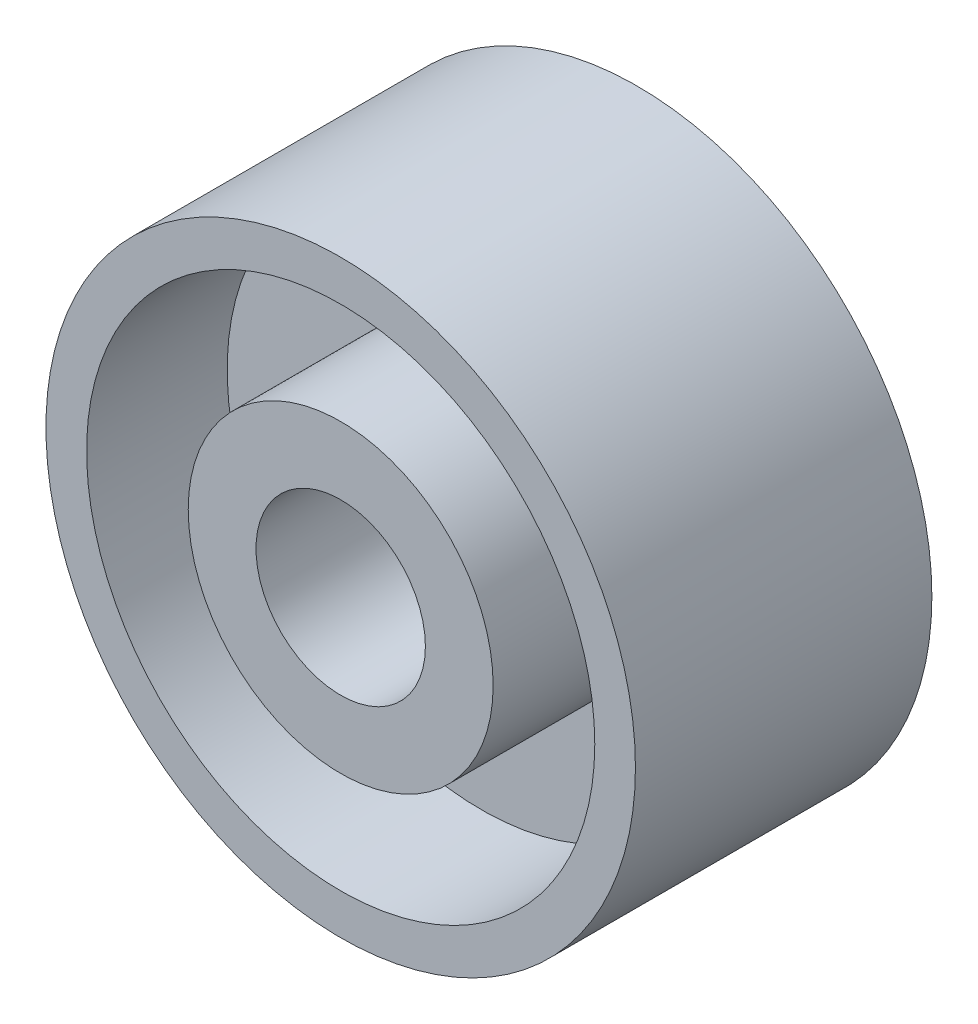
SolidWorks part; units mm, degrees
ref_plane "Front Plane" through (0, 0, 0) normal (0, 0, 1) x (1, 0, 0)
ref_plane "Top Plane" through (0, 0, 0) normal (0, 1, 0) x (1, 0, 0)
ref_plane "Right Plane" through (0, 0, 0) normal (1, 0, 0) x (0, 0, -1)
sketch "Sketch1" plane through (0, 0, 0) normal (0, 0, 1) x (1, 0, 0)
  line L0 (0, 0) -> (0, 2.4926) construction
  line L1 (0, 2.4926) -> (0, -2.9172) construction
  line L2 (0, 0) -> (4.0402, 0) construction
  line L3 (4.0402, 0) -> (-4.0539, 0) construction
  circle A0 centre (0, 0) radius 1.74
  dimension "D1" = 3.48
extrude "Boss-Extrude1" add sketch "Sketch1" against normal blind 0.875
sketch "Sketch2" plane through (0, 0, 0) normal (0, 0, 1) x (1, 0, 0)
  circle A0 centre (0, 0) radius 0.5
  dimension "D1" = 1
extrude "Cut-Extrude1" cut sketch "Sketch2" against normal through all
sketch "Sketch3" plane through (0, 0, 0) normal (0, 0, 1) x (1, 0, 0)
  circle A0 centre (0, 0) radius 0.75
  circle A1 centre (0, 0) radius 0.9
  circle A2 centre (0, 0) radius 1.5
  dimension "D1" = 1.5
  dimension "D2" = 1.8
  dimension "D3" = 3
extrude "Cut-Extrude2" cut sketch "Sketch3" against normal blind 0.83 contours A2 A1
mirror "Mirror3" about plane through (0, 0, -0.875) normal (0, 0, 1) of bodies 103
